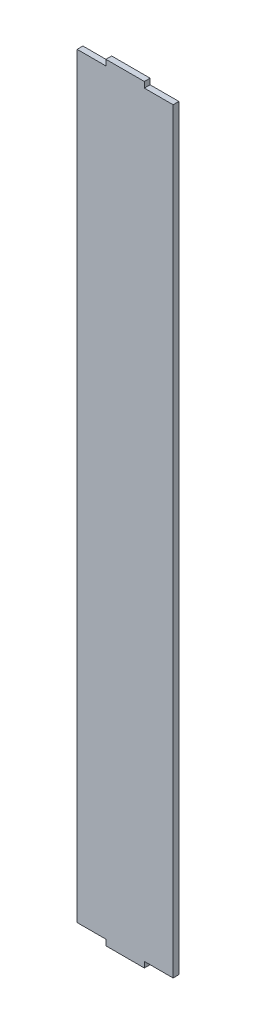
SolidWorks part; units mm, degrees
ref_plane "Alzado" through (0, 0, 0) normal (0, 0, 1) x (1, 0, 0)
ref_plane "Planta" through (0, 0, 0) normal (0, 1, 0) x (1, 0, 0)
ref_plane "Vista lateral" through (0, 0, 0) normal (1, 0, 0) x (0, 0, -1)
sketch "Croquis1" plane through (0, 0, 0) normal (0, 0, 1) x (1, 0, 0)
  line L0 (0, 0) -> (15, 0)
  line L1 (50, 0) -> (50, 394)
  line L2 (50, 394) -> (35, 394)
  line L3 (0, 394) -> (0, 0)
  line L4 (0, 0) -> (15, 0)
  line L5 (15, 0) -> (15, -3)
  line L6 (15, -3) -> (35, -3)
  line L7 (35, -3) -> (35, 0)
  line L8 (0, 394) -> (15, 394)
  line L9 (15, 394) -> (15, 397)
  line L10 (15, 397) -> (35, 397)
  line L11 (35, 397) -> (35, 394)
  line L12 (35, 0) -> (50, 0)
  dimension "D1" = 394
  dimension "D2" = 50
  dimension "D3" = 50
  dimension "D4" = 20
  dimension "D5" = 3
  dimension "D6" = 15
  dimension "D7" = 20
  dimension "D8" = 15
  dimension "D9" = 3
extrude "Saliente-Extruir3" add sketch "Croquis1" along normal blind 3 contours L7 L12 L1 L2 L11 L10 L9 L8 L3 L0 L5 L6
